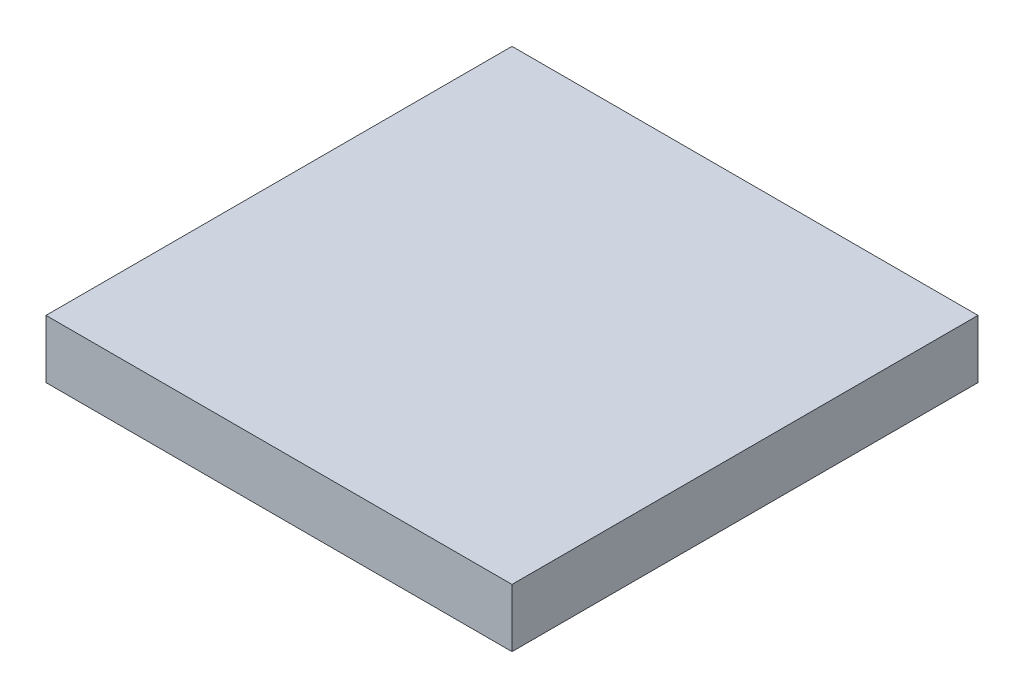
SolidWorks part; units mm, degrees
ref_plane "Front Plane" through (0, 0, 0) normal (0, 0, 1) x (1, 0, 0)
ref_plane "Top Plane" through (0, 0, 0) normal (0, 1, 0) x (1, 0, 0)
ref_plane "Right Plane" through (0, 0, 0) normal (1, 0, 0) x (0, 0, -1)
sketch "Sketch1" plane through (0, 0, 0) normal (0, 1, 0) x (1, 0, 0)
  line L1 (0, 8) -> (8, 8)
  line L2 (0, 8) -> (0, 0)
  line L3 (0, 0) -> (8, 0)
  line L4 (8, 8) -> (8, 0)
  point P4 (0, 0)
  dimension "D1" = 8
  dimension "D2" = 8
extrude "Boss-Extrude1" add sketch "Sketch1" along normal blind 1
